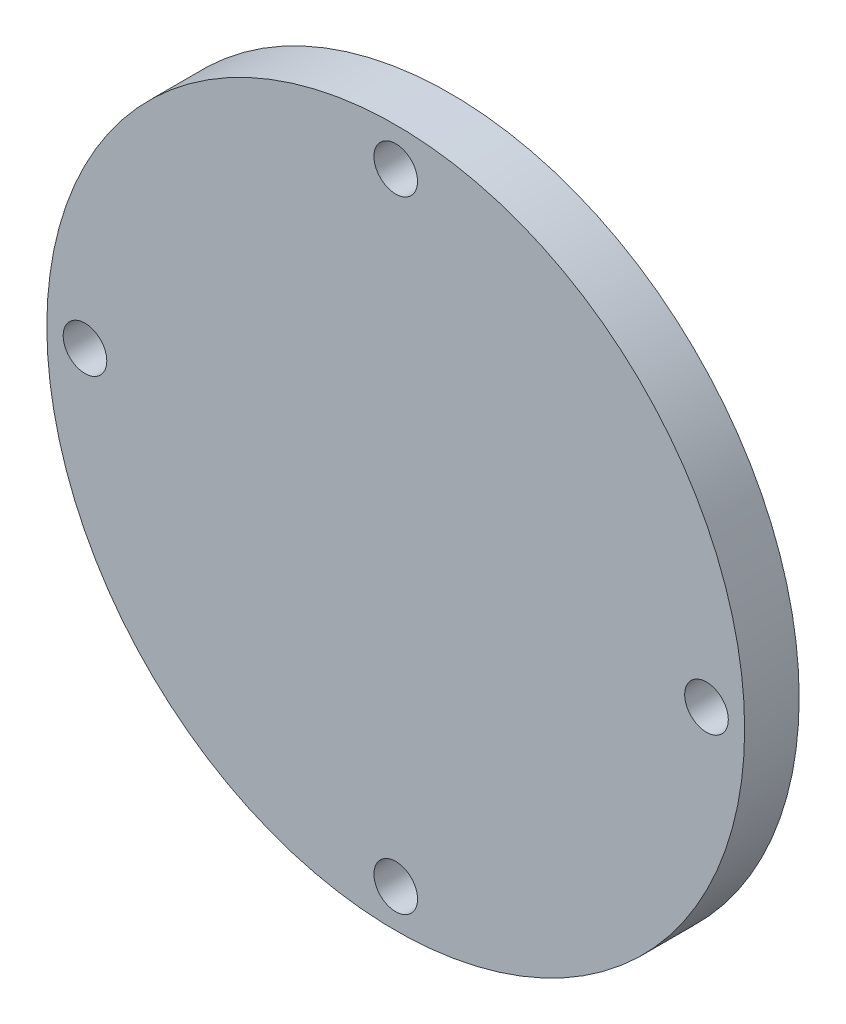
SolidWorks part; units mm, degrees
ref_plane "Front Plane" through (0, 0, 0) normal (0, 0, 1) x (1, 0, 0)
ref_plane "Top Plane" through (0, 0, 0) normal (0, 1, 0) x (1, 0, 0)
ref_plane "Right Plane" through (0, 0, 0) normal (1, 0, 0) x (0, 0, -1)
sketch "Sketch1" plane through (0, 0, 0) normal (0, 0, 1) x (1, 0, 0)
  circle A0 centre (0, 0) radius 32
  circle A1 centre (0, 28.5) radius 2
  circle A2 centre (28.5, 0) radius 2
  circle A3 centre (0, -28.5) radius 2
  circle A4 centre (-28.5, 0) radius 2
  point P13 (0, 0)
  dimension "D1" = 28.5
  dimension "D2" = 4
  dimension "D3" = 4
extrude "Boss-Extrude1" add sketch "Sketch1" along normal blind 5
